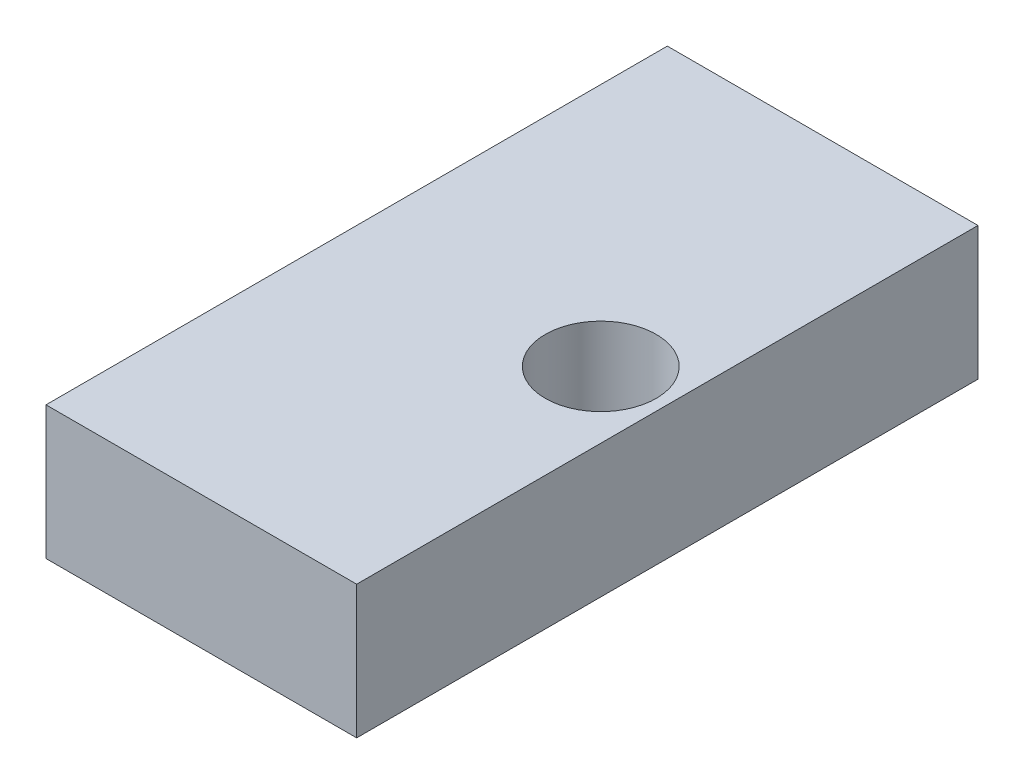
SolidWorks part; units mm, degrees
material "Pine"
ref_plane "Front Plane" through (0, 0, 0) normal (0, 0, 1) x (1, 0, 0)
ref_plane "Top Plane" through (0, 0, 0) normal (0, 1, 0) x (1, 0, 0)
ref_plane "Right Plane" through (0, 0, 0) normal (1, 0, 0) x (0, 0, -1)
sketch "Sketch1" plane through (0, 0, 0) normal (0, 0, 1) x (1, 0, 0)
  line L1 (-22.225, 9.525) -> (22.225, 9.525)
  line L2 (-22.225, 9.525) -> (-22.225, -9.525)
  line L3 (-22.225, -9.525) -> (22.225, -9.525)
  line L4 (22.225, 9.525) -> (22.225, -9.525)
  line L5 (-22.225, 9.525) -> (22.225, -9.525) construction
  line L6 (-22.225, -9.525) -> (22.225, 9.525) construction
  point P0 (0, 0)
  dimension "D1" = 44.45
  dimension "D2" = 19.05
extrude "Boss-Extrude1" add sketch "Sketch1" against normal blind 88.9
sketch "Sketch3" plane through (0, 9.525, 0) normal (0, 1, 0) x (1, 0, 0)
  circle A0 centre (12.7, 44.45) radius 7.9375
extrude "Cut-Extrude1" cut sketch "Sketch3" against normal through all
